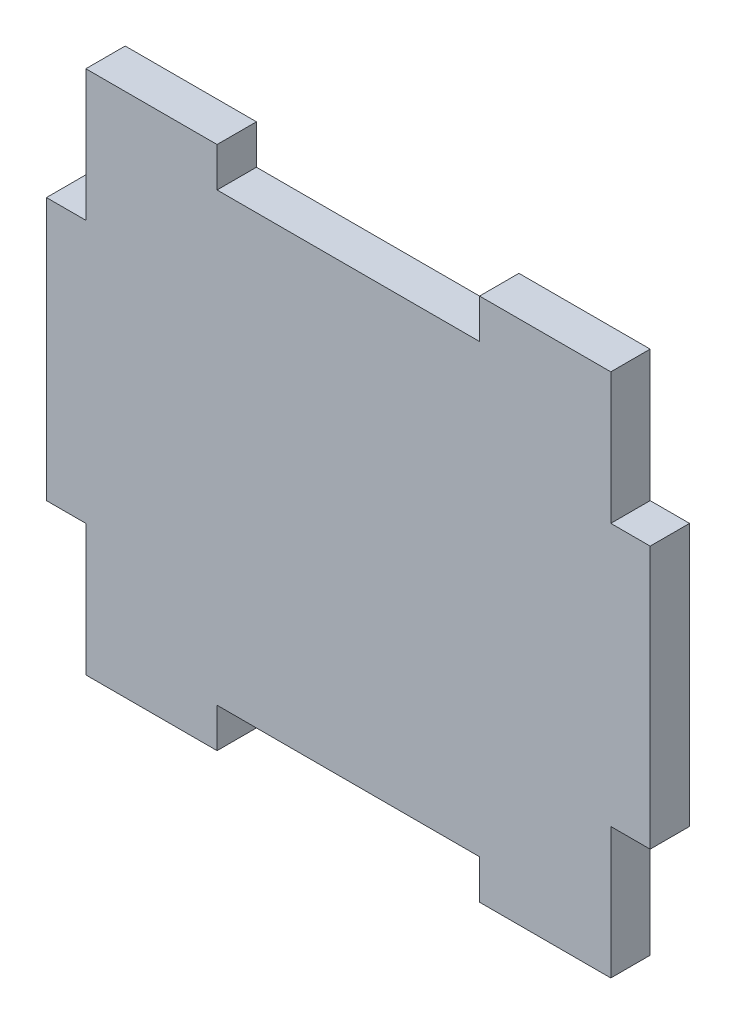
SolidWorks part; units mm, degrees
ref_plane "Alzado" through (0, 0, 0) normal (0, 0, 1) x (1, 0, 0)
ref_plane "Planta" through (0, 0, 0) normal (0, 1, 0) x (1, 0, 0)
ref_plane "Vista lateral" through (0, 0, 0) normal (1, 0, 0) x (0, 0, -1)
sketch "Croquis1" plane through (0, 0, 0) normal (0, 0, 1) x (1, 0, 0)
  line L0 (1.0999, 20.849) -> (1.0999, -19.151) construction
  line L1 (-18.9001, 20.849) -> (21.0999, 20.849)
  line L2 (-18.9001, -9.151) -> (-18.9001, -19.151)
  line L3 (-18.9001, -19.151) -> (21.0999, -19.151)
  line L5 (-18.9001, 10.849) -> (-21.9001, 10.849)
  line L7 (-18.9001, -9.151) -> (-21.9001, -9.151)
  line L8 (-21.9001, 10.849) -> (-21.9001, -9.151)
  line L9 (24.0999, 10.849) -> (24.0999, -9.151)
  line L10 (21.0999, -9.151) -> (24.0999, -9.151)
  line L12 (21.0999, 10.849) -> (24.0999, 10.849)
  line L13 (-18.9001, 10.849) -> (-18.9001, 20.849)
  line L14 (21.0999, 20.849) -> (21.0999, 10.849)
  line L15 (21.0999, -9.151) -> (21.0999, -19.151)
  dimension "D1" = 40
  dimension "D2" = 20
  dimension "40" = 40
  dimension "D3" = 3
  dimension "D4" = 10
extrude "Saliente-Extruir1" add sketch "Croquis1" along normal blind 3
sketch "Croquis6" plane through (0, 0, 3) normal (0, 0, 1) x (1, 0, 0)
  line L0 (21.0999, 20.849) -> (-18.9001, 20.849) construction
  line L1 (-8.9001, 20.849) -> (11.0999, 20.849)
  line L2 (-8.9001, 20.849) -> (-8.9001, 17.849)
  line L3 (-8.9001, 17.849) -> (11.0999, 17.849)
  line L4 (11.0999, 20.849) -> (11.0999, 17.849)
  line L5 (21.0999, 10.849) -> (21.0999, 20.849) construction
  line L6 (-21.9001, 0.849) -> (24.0999, 0.849) construction
  line L7 (-21.9001, 10.849) -> (-21.9001, -9.151) construction
  line L8 (24.0999, -9.151) -> (24.0999, 10.849) construction
  line L9 (11.0999, -19.151) -> (11.0999, -16.151)
  line L10 (-8.9001, -16.151) -> (11.0999, -16.151)
  line L11 (-8.9001, -19.151) -> (-8.9001, -16.151)
  line L12 (-8.9001, -19.151) -> (11.0999, -19.151)
  dimension "D1" = 3
  dimension "D2" = 20
  dimension "D3" = 10
extrude "Cortar-Extruir2" cut sketch "Croquis6" against normal blind 3
